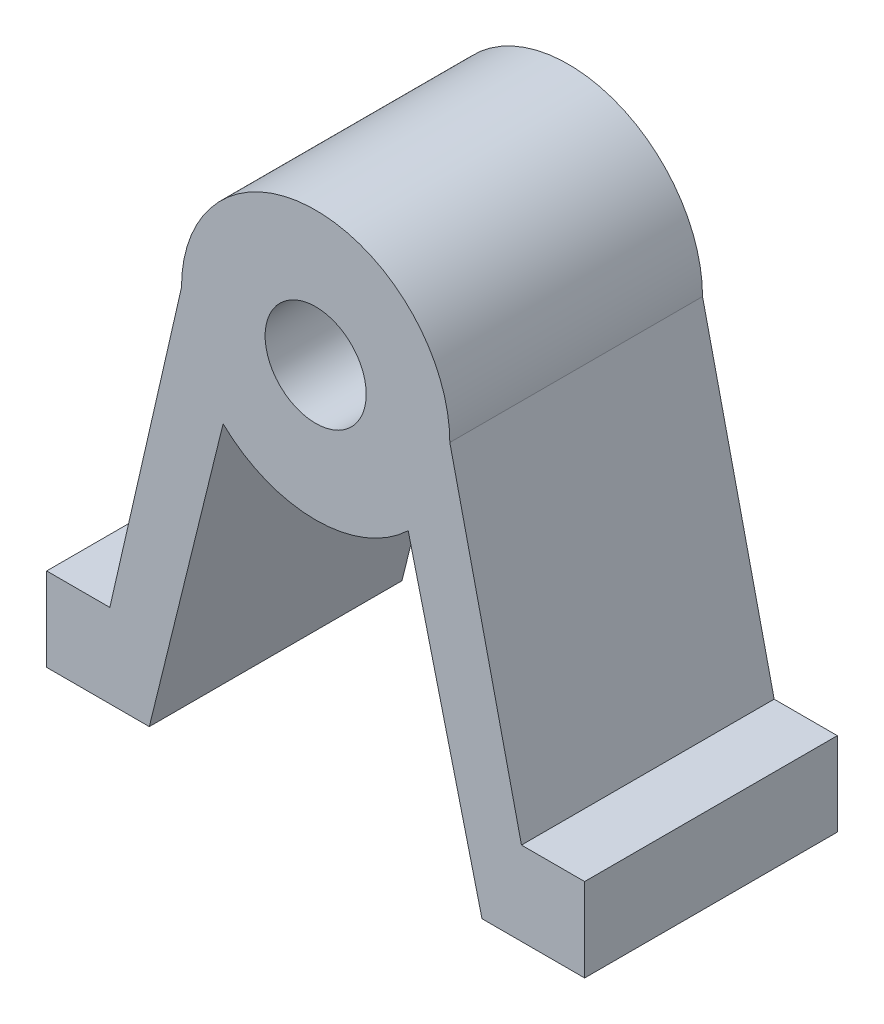
SolidWorks part; units mm, degrees
ref_plane "前视基准面" through (0, 0, 0) normal (0, 0, 1) x (1, 0, 0)
ref_plane "上视基准面" through (0, 0, 0) normal (0, 1, 0) x (1, 0, 0)
ref_plane "右视基准面" through (0, 0, 0) normal (1, 0, 0) x (0, 0, -1)
sketch "草图1" plane through (0, 0, 0) normal (0, 0, 1) x (1, 0, 0)
  line L0 (-48.3393, 5.3297) -> (-48.3393, 36.6997) construction
  line L1 (-37.7193, 36.6997) -> (-32.0497, 11.941)
  line L2 (-32.0497, 11.941) -> (-27.0497, 11.941)
  line L3 (-27.0497, 11.941) -> (-27.0497, 5.3297)
  line L4 (-27.0497, 5.3297) -> (-35.1736, 5.3297)
  line L5 (-41.0152, 29.0093) -> (-35.1736, 5.3297)
  line L6 (-55.6634, 29.0093) -> (-61.5049, 5.3297)
  line L7 (-69.6289, 5.3297) -> (-61.5049, 5.3297)
  line L8 (-69.6289, 11.941) -> (-69.6289, 5.3297)
  line L9 (-64.6289, 11.941) -> (-69.6289, 11.941)
  line L10 (-58.9593, 36.6997) -> (-64.6289, 11.941)
  circle A0 centre (-48.3393, 36.6997) radius 4
  arc A2 (-55.6634, 29.0093) -> (-41.0152, 29.0093) centre (-48.3393, 36.6997) ccw
  arc A3 (-37.7193, 36.6997) -> (-58.9593, 36.6997) centre (-48.3393, 36.6997) ccw
extrude "凸台-拉伸1" add sketch "草图1" along normal blind 20
